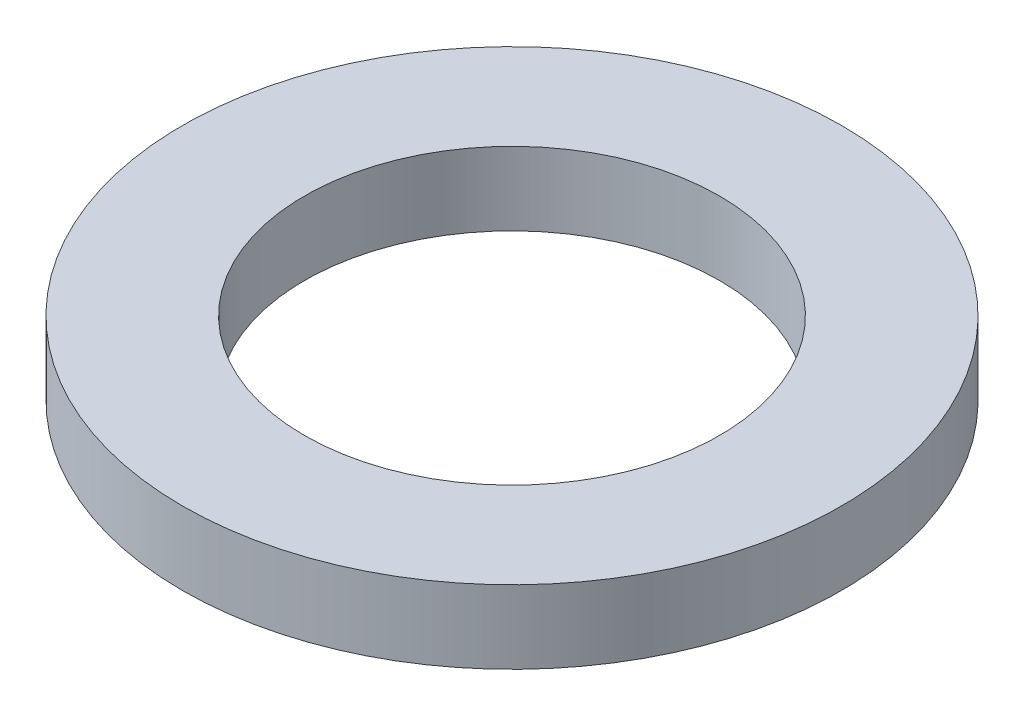
SolidWorks part; units mm, degrees
ref_plane "Front Plane" through (0, 0, 0) normal (0, 0, 1) x (1, 0, 0)
ref_plane "Top Plane" through (0, 0, 0) normal (0, 1, 0) x (1, 0, 0)
ref_plane "Right Plane" through (0, 0, 0) normal (1, 0, 0) x (0, 0, -1)
sketch "Sketch1" plane through (0, 0, 0) normal (0, 1, 0) x (1, 0, 0)
  circle A0 centre (0, 0) radius 8.5
  circle A1 centre (0, 0) radius 13.5
  dimension "D1" = 17
  dimension "D2" = 27
extrude "Boss-Extrude1" add sketch "Sketch1" along normal blind 3
